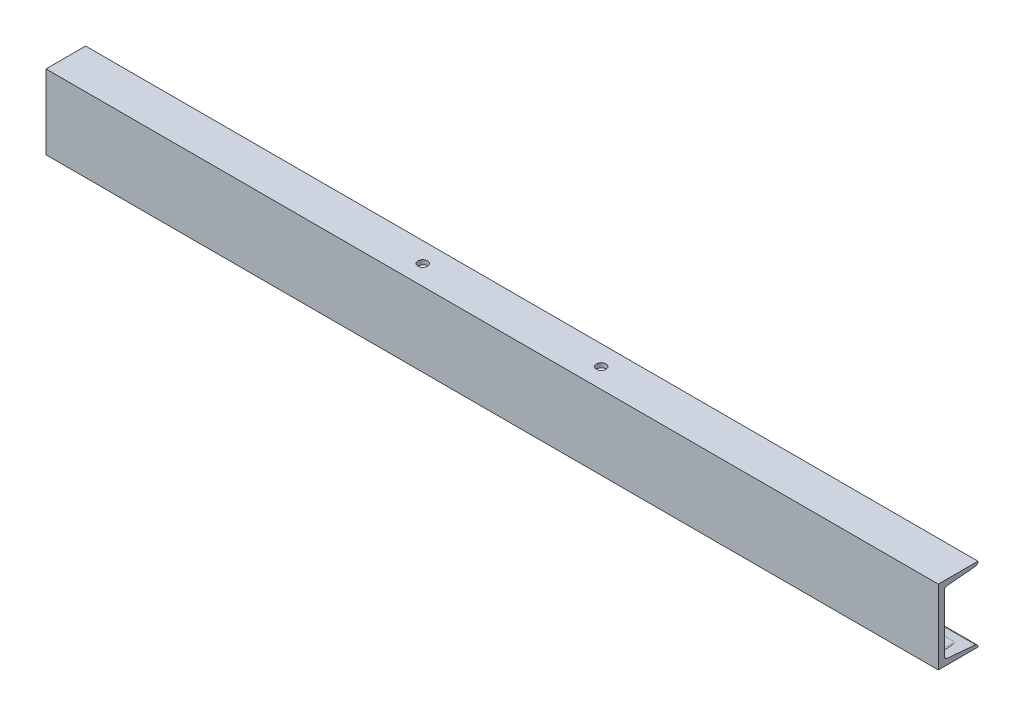
SolidWorks part; units mm, degrees
material "Plain Carbon Steel"
ref_plane "Front Plane" through (0, 0, 0) normal (0, 0, 1) x (1, 0, 0)
ref_plane "Top Plane" through (0, 0, 0) normal (0, 1, 0) x (1, 0, 0)
ref_plane "Right Plane" through (0, 0, 0) normal (1, 0, 0) x (0, 0, -1)
sketch "Sketch1" plane through (0, 0, 0) normal (0, 1, 0) x (1, 0, 0)
  line L0 (-450, 0) -> (450, 0)
  dimension "D1" = 900
other "Structural Member1"
ref_plane "Plane1" through (-450, 0, 0) normal (1, 0, 0) x (0, 0, 1)
sketch "Sketch17" plane through (-450, 0, 0) normal (1, 0, 0) x (0, 0, 1)
  line L0 (0, 37.5) -> (0, -37.5)
  line L1 (0, 37.5) -> (-40, 37.5)
  line L2 (0, -37.5) -> (-40, -37.5)
  line L3 (-6, 28.7531) -> (-6, -28.7531)
  line L4 (-8.7363, 31.7414) -> (-37.2637, 34.2586)
  line L5 (0, 0) -> (-48.9646, 0) construction
  line L6 (-40, 37.2469) -> (-40, 37.5)
  line L7 (-8.7363, -31.7414) -> (-37.2637, -34.2586)
  line L8 (-40, -37.2469) -> (-40, -37.5)
  arc A0 (-6, 28.7531) -> (-8.7363, 31.7414) centre (-9, 28.7531) ccw
  arc A1 (-37.2637, 34.2586) -> (-40, 37.2469) centre (-37, 37.2469) cw
  arc A2 (-6, -28.7531) -> (-8.7363, -31.7414) centre (-9, -28.7531) cw
  arc A3 (-37.2637, -34.2586) -> (-40, -37.2469) centre (-37, -37.2469) ccw
  point P6 (0, 0)
  point P12 (-6, 31.5)
  point P15 (-40, 34.5)
  dimension "D6" = 3
  dimension "D1" = 75
  dimension "D2" = 40
  dimension "D3" = 6
  dimension "D4" = 3
  dimension "D5" = 6
sketch "Sketch12" plane through (0, 0, 0) normal (0, 1, 0) x (1, 0, 0)
  line L0 (-412.5239, 20) -> (413.742, 20) construction
  line L1 (-450, 0) -> (450, 0) construction
  line L2 (0, 0) -> (0, 45.9021) construction
  line L4 (-450, 40) -> (-450, 0) construction
  circle A0 centre (-425, 20) radius 4.7625
  circle A1 centre (425, 20) radius 4.7625
  dimension "D2" = 9.525
  dimension "D1" = 20
  dimension "D3" = 25
extrude "Cut-Extrude1" cut sketch "Sketch12" against normal through all
sketch "Sketch15" plane through (0, 0, -6) normal (0, 0, -1) x (-1, 0, 0)
  line L0 (-425, 105.8991) -> (-425, -40.4286) construction
  line L1 (-375.1366, -28.5) -> (-474.8634, -28.5) construction
  line L3 (-412.5, -28.5) -> (-437.5, -28.5) construction
  line L4 (-412.5, -33.5) -> (-437.5, -33.5)
  line L5 (-412.5, -23.5) -> (-437.5, -23.5)
  line L6 (0, 0) -> (0, -58.1771) construction
  line L7 (412.5, -28.5) -> (437.5, -28.5) construction
  line L8 (412.5, -33.5) -> (437.5, -33.5)
  line L9 (412.5, -23.5) -> (437.5, -23.5)
  line L10 (-450, -37.5) -> (450, -37.5) construction
  arc A0 (-412.5, -33.5) -> (-412.5, -23.5) centre (-412.5, -28.5) ccw
  arc A1 (-437.5, -23.5) -> (-437.5, -33.5) centre (-437.5, -28.5) ccw
  arc A2 (412.5, -33.5) -> (412.5, -23.5) centre (412.5, -28.5) cw
  arc A3 (437.5, -23.5) -> (437.5, -33.5) centre (437.5, -28.5) cw
  ellipse E0 centre (-425, 32.7353) end of major axis (-429.7625, 32.7353) minor radius 0.4202 construction
  point P0 (-425, 32.7353)
  point P11 (-425, -28.5)
  point P16 (-425, -28.5)
  point P26 (425, -28.5)
  dimension "D2" = 5
  dimension "D1" = 9
  dimension "D3" = 25
extrude "Cut-Extrude2" cut sketch "Sketch15" along normal blind 40
sketch "Sketch18" plane through (0, 37.5, 0) normal (0, 1, 0) x (1, 0, 0)
  line L0 (-459.1181, 20) -> (466.5317, 20) construction
  line L1 (450, 0) -> (-450, 0) construction
  circle A0 centre (90, 20) radius 4.7625
  circle A1 centre (-90, 20) radius 4.7625
  dimension "D2" = 9.525
  dimension "D1" = 20
  dimension "D3" = 90
  dimension "D4" = 90
extrude "Cut-Extrude3" cut sketch "Sketch18" against normal blind 10
